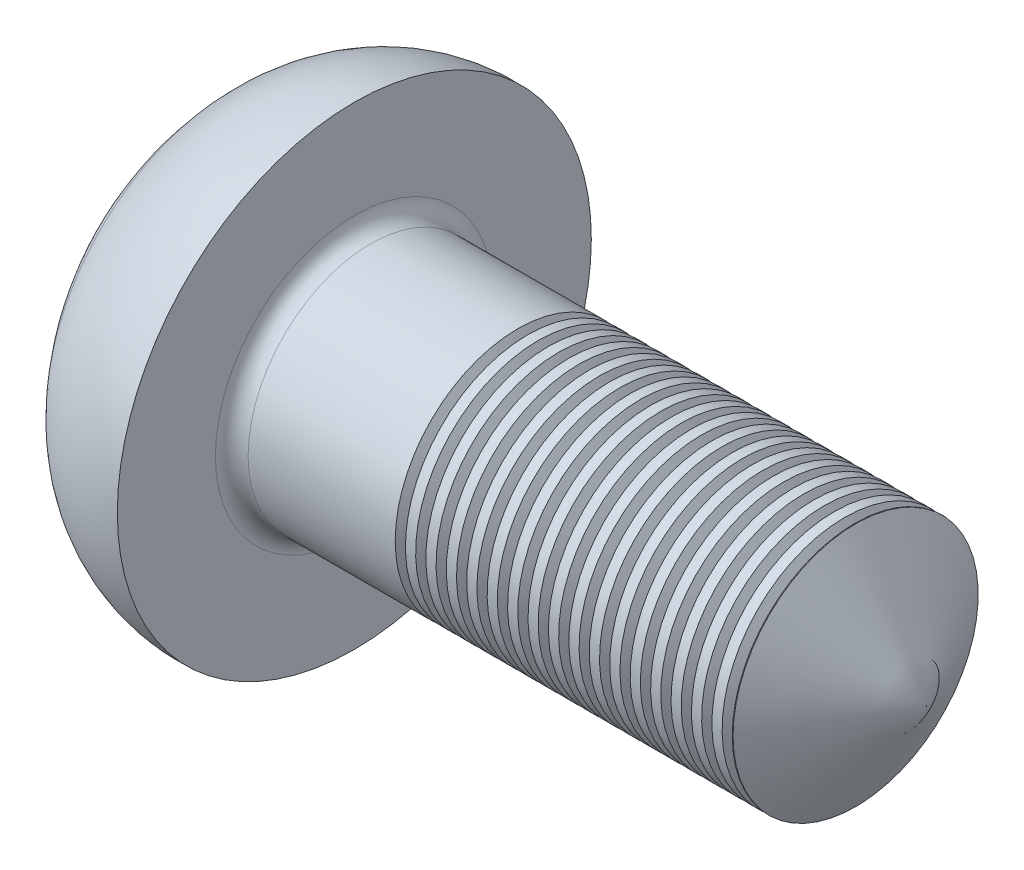
SolidWorks part; units mm, degrees
ref_plane "Front" through (0, 0, 0) normal (0, 0, 1) x (1, 0, 0)
ref_plane "Top" through (0, 0, 0) normal (0, 1, 0) x (1, 0, 0)
ref_plane "Right" through (0, 0, 0) normal (1, 0, 0) x (0, 0, -1)
sketch "Sketch1" plane through (0, 0, 0) normal (0, 1, 0) x (1, 0, 0)
  line L0 (-13.6293, 0) -> (11.3577, 0) construction
  line L1 (2.37, 1.5) -> (9.37, 1.5)
  line L2 (9.37, 1.5) -> (9.37, 0)
  line L3 (2.37, 1.5) -> (2.37, 2.9)
  line L4 (9.37, 0) -> (0, 0)
  arc A0 (2.37, 2.9) -> (0.8698, 2.2711) centre (2.2837, 1.002) ccw
  arc A1 (0, 0) -> (0.8698, 2.2711) centre (3.4, 0) cw
  dimension "r2" = 1.9
  dimension "r1" = 3.4
  dimension "d" = 3
  dimension "dk" = 5.8
  dimension "k" = 2.37
  dimension "l" = 7
revolve "Revolve1" add sketch "Sketch1" angle 360 about L0
cosmetic thread "ThreadCosmetic1" [suppressed] parameters "l0"=3.5, "dm"=2.75
fillet "Fillet2" radius 0.2 1 edges at (2.37, 0, 1.5)
sketch "Sketch4" plane through (0, 0, 0) normal (0, 1, 0) x (1, 0, 0)
  line L0 (4.7828, 0) -> (7.1391, 0) construction
  line L2 (10.1035, 0) -> (10.1035, 21)
  line L3 (10.1035, 21) -> (-2.7544, 21)
  line L4 (-2.7544, 21) -> (9.37, 0)
  line L5 (9.37, 0) -> (10.1035, 0)
  line L7 (9.37, -1.5) -> (9.37, 1.5) construction
  dimension "D1" = 60
  dimension "D2" = 0.7335
  dimension "D3" = 21
revolve "Cut-Revolve1" cut sketch "Sketch4" angle 360 about L0
sketch "Sketch2" plane through (0, 0, 0) normal (1, 0, 0) x (0, 0, -1)
  line L0 (-2.278, 0) -> (2.6944, 0) construction
  line L1 (0, -2.1234) -> (0, 2.1948) construction
  line L2 (-0.4625, 0.4625) -> (-1.85, 0.4625)
  line L3 (0.4625, -1.85) -> (-0.4625, -1.85)
  line L4 (0.4625, -1.85) -> (0.4625, -0.4625)
  line L5 (0.4625, 1.85) -> (-0.4625, 1.85)
  line L6 (-0.4625, -1.85) -> (-0.4625, -0.4625)
  line L7 (1.85, 0.4625) -> (0.4625, 0.4625)
  line L8 (1.85, 0.4625) -> (1.85, -0.4625)
  line L9 (1.85, -0.4625) -> (0.4625, -0.4625)
  line L10 (-1.85, 0.4625) -> (-1.85, -0.4625)
  line L11 (-0.4625, 0.4625) -> (-0.4625, 1.85)
  line L12 (-0.4625, -0.4625) -> (-1.85, -0.4625)
  line L13 (0.4625, 0.4625) -> (0.4625, 1.85)
  point P19 (-0.4625, 0.4625)
  point P22 (0.4625, 0.4625)
  point P27 (-0.4625, -0.4625)
  dimension "m" = 3.7
  dimension "D2" = 3.7
  dimension "D3" = 0.925
  dimension "D4" = 0.925
ref_plane "Plane1" through (2.62, 0, 0) normal (1, 0, 0) x (0, 0, -1)
sketch "Sketch5" plane through (2.62, 0, 0) normal (1, 0, 0) x (0, 0, -1)
  point P0 (0, 0)
loft "Cut-Loft1" cut profiles "Sketch5", "Sketch2"
sketch "Sketch6" plane through (0, 0, 0) normal (0, 0, 1) x (1, 0, 0)
  line L0 (4.37, 1.7) -> (4.495, 1.7)
  line L1 (4.495, 1.7) -> (4.495, 1.5)
  line L2 (4.495, 1.5) -> (4.4325, 1.3917)
  line L3 (4.37, 1.5) -> (4.4325, 1.3917)
  line L4 (4.37, 1.7) -> (4.37, 1.5)
  line L5 (10.7743, 0) -> (0, 0) construction
  line L6 (4.37, 1.5) -> (4.495, 1.5) construction
  line L7 (4.4325, 1.5) -> (4.4325, 1.3917) construction
  line L8 (8.504, 1.5) -> (2.57, 1.5) construction
  point P5 (4.4325, 1.7)
  dimension "D1" = 0.2
  dimension "D2" = 0.125
  dimension "D3" = 5
revolve "Cut-Revolve10" cut sketch "Sketch6" angle 360 about L5
pattern_linear "LPattern10" count 20 spacing 0.25 along (1, 0, 0) of "Cut-Revolve10"
equation "\"D4@Sketch2\" = \"D3@Sketch2\""
equation "\"D2@Sketch2\" = \"m@Sketch2\""
equation "\"D3@Sketch2\" = \"m@Sketch2\" / 4"
equation "\"D2@Sketch6\" = (  \"d@Sketch1\" - \"dm@ThreadCosmetic1\" )  / 2"
equation "\"D3@Sketch6\" = \"l0@ThreadCosmetic1\" + \"d@Sketch1\" / 2"
equation "\"D3@LPattern10\" = \"D2@Sketch6\" *2"
equation "\"D1@LPattern10\" = \"D3@Sketch6\" / \"D3@LPattern10\""
